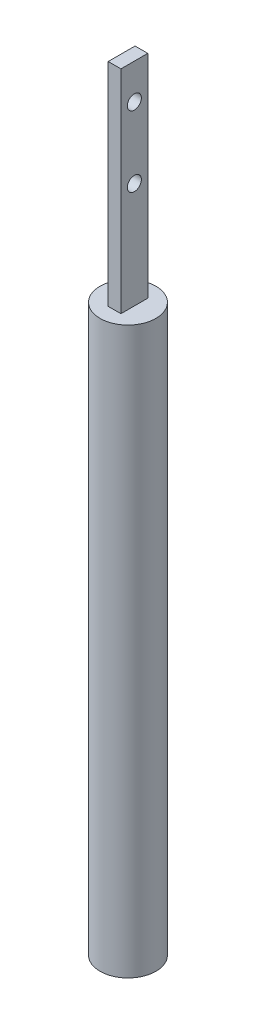
SolidWorks part; units mm, degrees
ref_plane "Front Plane" through (0, 0, 0) normal (0, 0, 1) x (1, 0, 0)
ref_plane "Top Plane" through (0, 0, 0) normal (0, 1, 0) x (1, 0, 0)
ref_plane "Right Plane" through (0, 0, 0) normal (1, 0, 0) x (0, 0, -1)
sketch "Sketch2" plane through (0, 0, 0) normal (0, 1, 0) x (1, 0, 0)
  circle A0 centre (0, 0) radius 3.95
extrude "Boss-Extrude1" add sketch "Sketch2" along normal blind 80
sketch "Sketch3" plane through (0, 80, 0) normal (0, 1, 0) x (1, 0, 0)
  line L1 (-0.9, -1.9) -> (0.9, -1.9)
  line L2 (-0.9, -1.9) -> (-0.9, 1.9)
  line L3 (-0.9, 1.9) -> (0.9, 1.9)
  line L4 (0.9, -1.9) -> (0.9, 1.9)
  line L5 (-0.9, -1.9) -> (0.9, 1.9) construction
  line L6 (-0.9, 1.9) -> (0.9, -1.9) construction
  point P0 (0, 0)
  dimension "D1" = 3.8
  dimension "D2" = 1.8
extrude "Boss-Extrude3" add sketch "Sketch3" along normal blind 30
sketch "Sketch5" plane through (0.9, 0, 0) normal (1, 0, 0) x (0, 0, -1)
  line L0 (0, 110) -> (0, 105) construction
  line L1 (-1.9, 110) -> (1.9, 110) construction
  line L2 (0, 105) -> (0, 95) construction
  circle A0 centre (0, 105) radius 1
  circle A1 centre (0, 95) radius 1
  dimension "D3" = 2
  dimension "D4" = 2
  dimension "D1" = 5
  dimension "D2" = 10
extrude "Cut-Extrude1" cut sketch "Sketch5" against normal up to surface (1.8 mm away) up to face at (-0.9, 95, 0)
